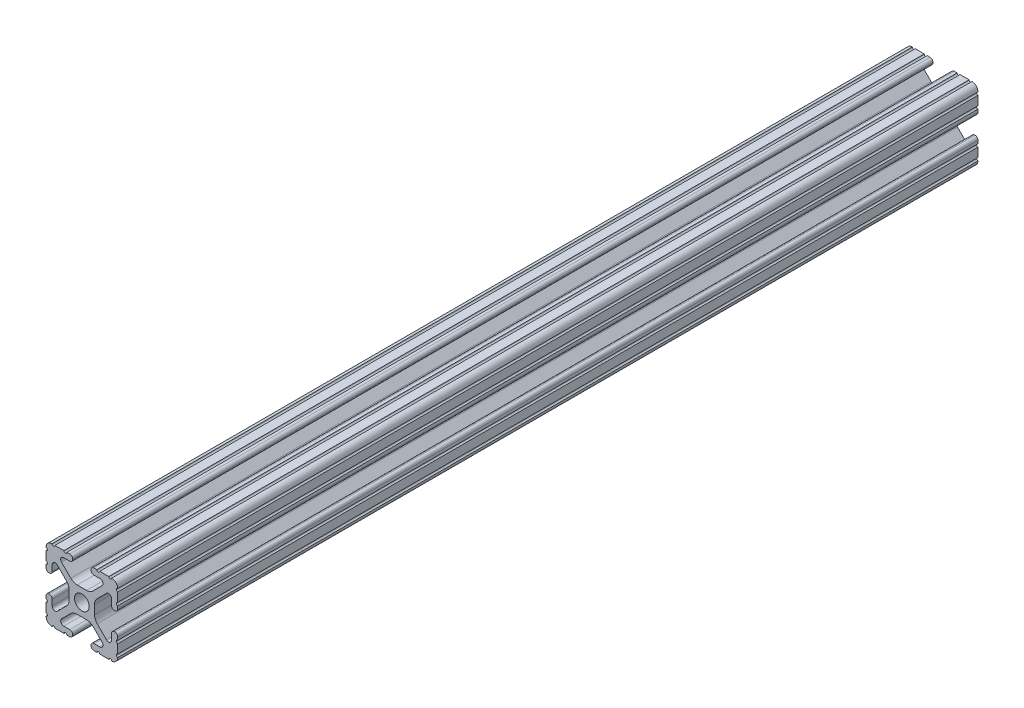
SolidWorks part; units mm, degrees
ref_plane "Front" through (0, 0, 0) normal (0, 0, 1) x (1, 0, 0)
ref_plane "Top" through (0, 0, 0) normal (0, 1, 0) x (1, 0, 0)
ref_plane "Right" through (0, 0, 0) normal (1, 0, 0) x (0, 0, -1)
sketch "Sketch1" plane through (0, 0, 0) normal (0, 0, 1) x (1, 0, 0)
  line L0 (-7.5107, 9.4563) -> (7.5107, 9.4563) construction
  line L1 (-7.4968, -9.4098) -> (7.4968, -9.4098) construction
  line L88 (-7.1797, -8.6452) -> (-3.9523, -5.4237)
  line L89 (-1.7093, -4.4958) -> (1.7093, -4.4958)
  line L90 (3.9523, -5.4237) -> (7.1797, -8.6452)
  line L91 (6.4164, -10.4902) -> (4.2875, -10.4902)
  line L92 (3.2385, -11.5392) -> (3.2385, -11.651)
  line L93 (4.2875, -12.7) -> (5.3171, -12.7)
  line L94 (6.3331, -12.7) -> (9.5504, -12.7)
  line L95 (12.7, -9.5504) -> (12.7, -6.3331)
  line L96 (12.7, -5.3171) -> (12.7, -4.2875)
  line L97 (11.651, -3.2385) -> (11.5392, -3.2385)
  line L98 (10.4902, -4.2875) -> (10.4902, -6.4021)
  line L99 (8.7371, -7.1294) -> (5.441, -3.8408)
  line L100 (4.5085, -1.5932) -> (4.5085, 1.5932)
  line L101 (5.441, 3.8408) -> (8.7371, 7.1294)
  line L102 (10.4902, 6.4021) -> (10.4902, 4.2875)
  line L103 (11.5392, 3.2385) -> (11.651, 3.2385)
  line L104 (12.7, 4.2875) -> (12.7, 5.3171)
  line L105 (12.7, 6.3331) -> (12.7, 9.5504)
  line L106 (9.5504, 12.7) -> (6.3331, 12.7)
  line L107 (5.3171, 12.7) -> (4.2875, 12.7)
  line L108 (3.2385, 11.651) -> (3.2385, 11.5392)
  line L109 (4.2875, 10.4902) -> (6.4768, 10.4902)
  line L110 (7.207, 8.7244) -> (3.8983, 5.4232)
  line L111 (1.6558, 4.4958) -> (-1.6558, 4.4958)
  line L112 (-3.8983, 5.4232) -> (-7.207, 8.7244)
  line L113 (-6.4768, 10.4902) -> (-4.2875, 10.4902)
  line L114 (-3.2385, 11.5392) -> (-3.2385, 11.651)
  line L115 (-4.2875, 12.7) -> (-5.3171, 12.7)
  line L116 (-6.3331, 12.7) -> (-9.5504, 12.7)
  line L117 (-12.7, 9.5504) -> (-12.7, 6.3331)
  line L118 (-12.7, 5.3171) -> (-12.7, 4.2875)
  line L119 (-11.651, 3.2385) -> (-11.5392, 3.2385)
  line L120 (-10.4902, 4.2875) -> (-10.4902, 6.4021)
  line L121 (-8.7371, 7.1294) -> (-5.441, 3.8408)
  line L122 (-4.5085, 1.5932) -> (-4.5085, -1.5932)
  line L123 (-5.441, -3.8408) -> (-8.7371, -7.1294)
  line L124 (-10.4902, -6.4021) -> (-10.4902, -4.2875)
  line L125 (-11.5392, -3.2385) -> (-11.651, -3.2385)
  line L126 (-12.7, -4.2875) -> (-12.7, -5.3171)
  line L127 (-12.7, -6.3331) -> (-12.7, -9.5504)
  line L128 (-9.5504, -12.7) -> (-6.3331, -12.7)
  line L129 (-5.3171, -12.7) -> (-4.2875, -12.7)
  line L130 (-3.2385, -11.651) -> (-3.2385, -11.5392)
  line L131 (-4.2875, -10.4902) -> (-6.4164, -10.4902)
  circle A1 centre (0, 0) radius 2.6035
  arc A104 (-7.1797, -8.6452) -> (-6.4164, -10.4902) centre (-6.4164, -9.4098) ccw
  arc A105 (-1.7093, -4.4958) -> (-3.9523, -5.4237) centre (-1.7093, -7.6708) ccw
  arc A106 (3.9523, -5.4237) -> (1.7093, -4.4958) centre (1.7093, -7.6708) ccw
  arc A107 (6.4164, -10.4902) -> (7.1797, -8.6452) centre (6.4164, -9.4098) ccw
  arc A108 (4.2875, -10.4902) -> (3.2385, -11.5392) centre (4.2875, -11.5392) ccw
  arc A109 (3.2385, -11.651) -> (4.2875, -12.7) centre (4.2875, -11.651) ccw
  arc A110 (6.3331, -12.7) -> (5.3171, -12.7) centre (5.8251, -12.7) ccw
  arc A111 (10.5664, -12.6998) -> (9.5504, -12.7) centre (10.0584, -12.7) ccw
  arc A112 (10.5664, -12.6998) -> (12.6998, -10.5664) centre (10.5918, -10.5918) ccw
  arc A113 (12.7, -9.5504) -> (12.6998, -10.5664) centre (12.7, -10.0584) ccw
  arc A114 (12.7, -5.3171) -> (12.7, -6.3331) centre (12.7, -5.8251) ccw
  arc A115 (12.7, -4.2875) -> (11.651, -3.2385) centre (11.651, -4.2875) ccw
  arc A116 (11.5392, -3.2385) -> (10.4902, -4.2875) centre (11.5392, -4.2875) ccw
  arc A117 (8.7371, -7.1294) -> (10.4902, -6.4021) centre (9.4628, -6.4021) ccw
  arc A118 (4.5085, -1.5932) -> (5.441, -3.8408) centre (7.6835, -1.5932) ccw
  arc A119 (5.441, 3.8408) -> (4.5085, 1.5932) centre (7.6835, 1.5932) ccw
  arc A120 (10.4902, 6.4021) -> (8.7371, 7.1294) centre (9.4628, 6.4021) ccw
  arc A121 (10.4902, 4.2875) -> (11.5392, 3.2385) centre (11.5392, 4.2875) ccw
  arc A122 (11.651, 3.2385) -> (12.7, 4.2875) centre (11.651, 4.2875) ccw
  arc A123 (12.7, 6.3331) -> (12.7, 5.3171) centre (12.7, 5.8251) ccw
  arc A124 (12.6998, 10.5664) -> (12.7, 9.5504) centre (12.7, 10.0584) ccw
  arc A125 (12.6998, 10.5664) -> (10.5664, 12.6998) centre (10.5918, 10.5918) ccw
  arc A126 (9.5504, 12.7) -> (10.5664, 12.6998) centre (10.0584, 12.7) ccw
  arc A127 (5.3171, 12.7) -> (6.3331, 12.7) centre (5.8251, 12.7) ccw
  arc A128 (4.2875, 12.7) -> (3.2385, 11.651) centre (4.2875, 11.651) ccw
  arc A129 (3.2385, 11.5392) -> (4.2875, 10.4902) centre (4.2875, 11.5392) ccw
  arc A130 (7.207, 8.7244) -> (6.4768, 10.4902) centre (6.4768, 9.4563) ccw
  arc A131 (1.6558, 4.4958) -> (3.8983, 5.4232) centre (1.6558, 7.6708) ccw
  arc A132 (-3.8983, 5.4232) -> (-1.6558, 4.4958) centre (-1.6558, 7.6708) ccw
  arc A133 (-6.4768, 10.4902) -> (-7.207, 8.7244) centre (-6.4768, 9.4563) ccw
  arc A134 (-4.2875, 10.4902) -> (-3.2385, 11.5392) centre (-4.2875, 11.5392) ccw
  arc A135 (-3.2385, 11.651) -> (-4.2875, 12.7) centre (-4.2875, 11.651) ccw
  arc A136 (-6.3331, 12.7) -> (-5.3171, 12.7) centre (-5.8251, 12.7) ccw
  arc A137 (-10.5664, 12.6998) -> (-9.5504, 12.7) centre (-10.0584, 12.7) ccw
  arc A138 (-10.5664, 12.6998) -> (-12.6998, 10.5664) centre (-10.5918, 10.5918) ccw
  arc A139 (-12.7, 9.5504) -> (-12.6998, 10.5664) centre (-12.7, 10.0584) ccw
  arc A140 (-12.7, 5.3171) -> (-12.7, 6.3331) centre (-12.7, 5.8251) ccw
  arc A141 (-12.7, 4.2875) -> (-11.651, 3.2385) centre (-11.651, 4.2875) ccw
  arc A142 (-11.5392, 3.2385) -> (-10.4902, 4.2875) centre (-11.5392, 4.2875) ccw
  arc A143 (-8.7371, 7.1294) -> (-10.4902, 6.4021) centre (-9.4628, 6.4021) ccw
  arc A144 (-4.5085, 1.5932) -> (-5.441, 3.8408) centre (-7.6835, 1.5932) ccw
  arc A145 (-5.441, -3.8408) -> (-4.5085, -1.5932) centre (-7.6835, -1.5932) ccw
  arc A146 (-10.4902, -6.4021) -> (-8.7371, -7.1294) centre (-9.4628, -6.4021) ccw
  arc A147 (-10.4902, -4.2875) -> (-11.5392, -3.2385) centre (-11.5392, -4.2875) ccw
  arc A148 (-11.651, -3.2385) -> (-12.7, -4.2875) centre (-11.651, -4.2875) ccw
  arc A149 (-12.7, -6.3331) -> (-12.7, -5.3171) centre (-12.7, -5.8251) ccw
  arc A150 (-12.6998, -10.5664) -> (-12.7, -9.5504) centre (-12.7, -10.0584) ccw
  arc A151 (-12.6998, -10.5664) -> (-10.5664, -12.6998) centre (-10.5918, -10.5918) ccw
  arc A152 (-9.5504, -12.7) -> (-10.5664, -12.6998) centre (-10.0584, -12.7) ccw
  arc A153 (-5.3171, -12.7) -> (-6.3331, -12.7) centre (-5.8251, -12.7) ccw
  arc A154 (-4.2875, -12.7) -> (-3.2385, -11.651) centre (-4.2875, -11.651) ccw
  arc A155 (-3.2385, -11.5392) -> (-4.2875, -10.4902) centre (-4.2875, -11.5392) ccw
extrude "Boss-Extrude1" add sketch "Sketch1" along normal mid plane 304.8
